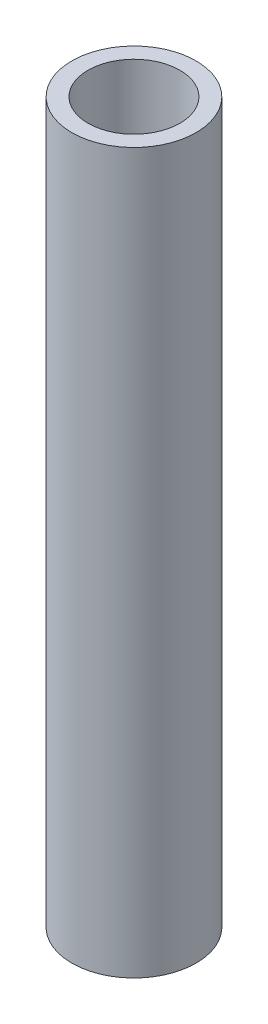
SolidWorks part; units mm, degrees
ref_plane "Front" through (0, 0, 0) normal (0, 0, 1) x (1, 0, 0)
ref_plane "Top" through (0, 0, 0) normal (0, 1, 0) x (1, 0, 0)
ref_plane "Right" through (0, 0, 0) normal (1, 0, 0) x (0, 0, -1)
sketch "Sketch1" plane through (0, 0, 0) normal (0, 1, 0) x (1, 0, 0)
  circle A0 centre (0, 0) radius 19.05
  dimension "D1" = 38.1
extrude "Boss-Extrude1" add sketch "Sketch1" along normal blind 220.472
sketch "Sketch2" plane through (0, 220.472, 0) normal (0, 1, 0) x (1, 0, 0)
  circle A0 centre (0, 0) radius 12.7
  dimension "D1" = 25.4
extrude "Cut-Extrude1" cut sketch "Sketch2" against normal through all
hole_wizard "1-1/4-7 Tapped Hole1" positions "Sketch6" profile "Sketch5" tap size "1-1/4-7" standard "ANSI Inch"
sketch "Sketch6" plane through (0, 220.472, 0) normal (0, 1, 0) x (1, 0, 0)
  point P0 (0, 0)
sketch "Sketch5" plane through (0, 220.472, 0) normal (1, 0, 0) x (0, 0, 1)
  line L0 (0, 0) -> (0, 57.4878)
  line L1 (0, 57.4878) -> (14.0894, 49.022)
  line L2 (14.0894, 49.022) -> (14.0894, 0)
  line L5 (14.0894, 0) -> (0, 0)
  line L10 (0, 57.4878) -> (-14.0894, 49.022) construction
  line L11 (0, -6.35) -> (0, 107.95) construction
  dimension "Tap Drill Dia." = 28.1788
  dimension "Tap Drill Depth" = 49.022
  dimension "Drill Angle" = 118
cosmetic thread "Hole Thread1" parameters "D1"=38.1, "D2"=31.75
hole_wizard "1-1/4-7 Tapped Hole2" positions "Sketch8" profile "Sketch7" tap size "1-1/4-7" standard "ANSI Inch"
sketch "Sketch8" plane through (0, 0, 0) normal (0, -1, 0) x (-1, 0, 0)
  point P0 (0, 0)
sketch "Sketch7" plane through (0, 0, 0) normal (1, 0, 0) x (0, 0, -1)
  line L0 (0, 0) -> (0, 57.4878)
  line L1 (0, 57.4878) -> (14.0894, 49.022)
  line L2 (14.0894, 49.022) -> (14.0894, 0)
  line L5 (14.0894, 0) -> (0, 0)
  line L10 (0, 57.4878) -> (-14.0894, 49.022) construction
  line L11 (0, -6.35) -> (0, 107.95) construction
  dimension "Tap Drill Dia." = 28.1788
  dimension "Tap Drill Depth" = 49.022
  dimension "Drill Angle" = 118
cosmetic thread "Hole Thread2" parameters "D1"=38.1, "D2"=31.75
